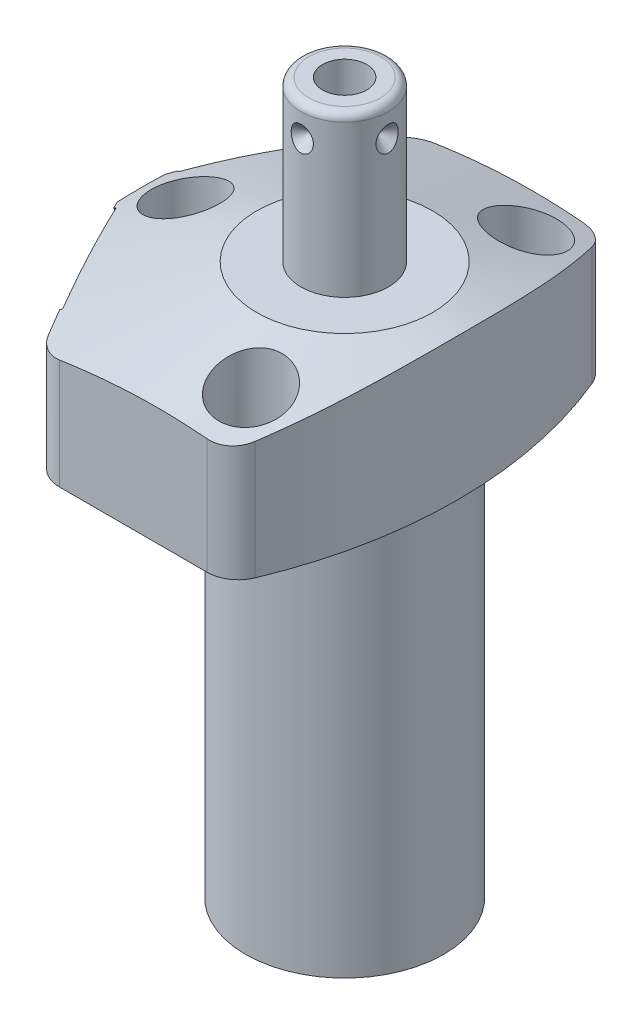
SolidWorks part; units mm, degrees
material "Alloy Steel"
ref_plane "Front Plane" through (0, 0, 0) normal (0, 0, 1) x (1, 0, 0)
ref_plane "Top Plane" through (0, 0, 0) normal (0, 1, 0) x (1, 0, 0)
ref_plane "Right Plane" through (0, 0, 0) normal (1, 0, 0) x (0, 0, -1)
ref_plane "Plane1" through (0, 0, 0) normal (0, 0, 1) x (0, -1, 0)
sketch "Sketch1" plane through (0, 0, 0) normal (0, 0, 1) x (0, -1, 0)
  line L0 (0, 28.575) -> (-19.05, 28.575)
  line L1 (-19.05, 28.575) -> (-19.05, 0)
  line L2 (-19.05, 0) -> (50.8, 0)
  line L3 (50.8, 0) -> (50.8, 12.573)
  line L4 (50.8, 12.573) -> (0, 12.573)
  line L5 (0, 12.573) -> (0, 28.575)
  line L6 (-22.5425, 0) -> (54.2925, 0) construction
  dimension "D1" = 69.85
  dimension "D2" = 19.05
  dimension "D3" = 25.146
  dimension "D4" = 57.15
revolve "Revolve1" add sketch "Sketch1" angle 360 about L6
ref_plane "Plane2" through (0, 0, 0) normal (0, -1, 0) x (0, 0, -1)
sketch "Sketch2" plane through (0, 0, 0) normal (0, -1, 0) x (0, 0, -1)
  line L0 (23.8125, -15.7954) -> (23.8125, 15.7954)
  line L2 (-23.8125, 15.7954) -> (-23.8125, -15.7954)
  line L3 (0, -18.0139) -> (0, 30.7935) construction
  arc A0 (23.8125, -15.7954) -> (23.8125, 15.7954) centre (0, 0) ccw
  circle A1 centre (0, 0) radius 28.575
  arc A2 (-23.8125, 15.7954) -> (-23.8125, -15.7954) centre (0, 0) ccw
  point P4 (0, 0)
  dimension "D1" = 47.625
  dimension "D2" = 0
extrude "Cut-Extrude1" cut sketch "Sketch2" against normal up to next
ref_plane "Plane3" through (0, 0, 0) normal (0, -1, 0) x (-1, 0, 0)
sketch "Sketch3" plane through (0, 0, 0) normal (0, -1, 0) x (-1, 0, 0)
  line L0 (14.7539, 23.8125) -> (27.4152, 0)
  line L1 (27.4152, 0) -> (14.7539, -23.8125)
  line L2 (-24.5787, -13.0687) -> (45.9515, 24.4329) construction
  line L3 (0, 0) -> (35.175, 0) construction
  line L4 (15.7954, -23.8125) -> (-15.7954, -23.8125) construction
  line L5 (-15.7954, 23.8125) -> (15.7954, 23.8125) construction
  line L6 (15.7954, -23.8125) -> (14.7539, -23.8125)
  line L7 (14.7539, 23.8125) -> (15.7954, 23.8125)
  arc A0 (15.7954, -23.8125) -> (15.7954, 23.8125) centre (0, 0) ccw construction
  arc A1 (15.7954, -23.8125) -> (15.7954, 23.8125) centre (0, 0) ccw
  dimension "D1" = 28
  dimension "D2" = 24.2062
extrude "Cut-Extrude2" cut sketch "Sketch3" against normal up to next
ref_plane "Plane4" through (0, 0, 0) normal (0, -1, 0) x (-1, 0, 0)
sketch "S2D0002" plane through (0, 0, 0) normal (0, -1, 0) x (-1, 0, 0)
  line L0 (25.8064, 53.3791) -> (25.8064, -53.3791)
  arc A0 (25.8064, 53.3791) -> (25.8064, -53.3791) centre (41.275, 0) ccw
  dimension "D1" = 55.5752
  dimension "D2" = 15.4686
  dimension "D3" = 41.275
extrude "Cut-Extrude3" cut sketch "S2D0002" against normal blind 26.035 flip side to cut
fillet "Fillet1" radius 3.9624 4 edges at (8.9402, 9.525, 23.8125) (-14.7539, 9.525, 23.8125) (-14.7539, 9.525, -23.8125) (8.9402, 9.525, -23.8125)
ref_plane "Plane5" through (0, 0, 0) normal (0, 0, 1) x (1, 0, 0)
sketch "Sketch5" plane through (0, 0, 0) normal (0, 0, 1) x (1, 0, 0)
  line L0 (-11.176, 19.05) -> (-44.45, 8.2386)
  line L1 (0, 5.9984) -> (0, 19.6715) construction
  line L2 (-15.8716, 19.05) -> (-25.8064, 19.05) construction
  line L3 (-11.176, 19.05) -> (-44.45, 19.05)
  line L4 (-44.45, 19.05) -> (-44.45, 8.2386)
  dimension "D1" = 22.352
  dimension "D2" = 18
  dimension "D3" = 44.45
revolve "Cut-Revolve1" cut sketch "Sketch5" angle 360 about L1
ref_plane "Plane6" through (-21.1485, 7.9502, -11.2449) normal (0, 1, 0) x (0.4695, 0, -0.8829)
sketch "Sketch6" plane through (-21.1485, 7.9502, -11.2449) normal (0, 1, 0) x (0.4695, 0, -0.8829)
  line L0 (0, 0) -> (4.5466, 0)
  line L1 (4.5466, 0) -> (4.1066, -2.0701)
  line L2 (4.1066, -2.0701) -> (3.4544, -2.7223)
  line L3 (3.4544, -2.7223) -> (3.4544, -12.192)
  line L4 (3.4544, -12.192) -> (0, -12.192)
  line L5 (0, -12.192) -> (0, 0)
  line L6 (0, -12.8016) -> (0, 0.6096) construction
  dimension "D1" = 12.192
revolve "Cut-Revolve2" cut sketch "Sketch6" angle 360 about L6
ref_plane "Plane7" through (-21.1485, 7.9502, 11.2449) normal (0, 1, 0) x (-0.4695, 0, -0.8829)
sketch "Sketch7" plane through (-21.1485, 7.9502, 11.2449) normal (0, 1, 0) x (-0.4695, 0, -0.8829)
  line L0 (0, 0) -> (4.5466, 0)
  line L1 (4.5466, 0) -> (4.1066, -2.0701)
  line L2 (4.1066, -2.0701) -> (3.4544, -2.7223)
  line L3 (3.4544, -2.7223) -> (3.4544, -12.192)
  line L4 (3.4544, -12.192) -> (0, -12.192)
  line L5 (0, -12.192) -> (0, 0)
  line L6 (0, -12.8016) -> (0, 0.6096) construction
  dimension "D1" = 12.192
revolve "Cut-Revolve3" cut sketch "Sketch7" angle 360 about L6
ref_plane "Plane8" through (-11.1252, 2.667, -15.875) normal (0, 0, 1) x (-1, 0, 0)
sketch "Sketch17" plane through (-21.3728, 0, 11.3641) normal (-0.8829, 0, 0.4695) x (0.4695, 0, 0.8829)
  circle A0 centre (0, 7.9502) radius 10.4775
  dimension "D1" = 20.955
extrude "Cut-Extrude4" cut sketch "Sketch17" against normal blind 0.254
sketch "Sketch18" plane through (-21.3728, 0, -11.3641) normal (-0.8829, 0, -0.4695) x (-0.4695, 0, 0.8829)
  circle A0 centre (0, 7.9502) radius 10.4775
  dimension "D1" = 20.955
extrude "Cut-Extrude5" cut sketch "Sketch18" against normal blind 0.254
sketch "Sketch8" plane through (-11.1252, 2.667, -15.875) normal (0, 0, 1) x (-1, 0, 0)
  line L0 (0, 0) -> (4.5466, 0)
  line L1 (4.5466, 0) -> (4.1066, -2.0701)
  line L2 (4.1066, -2.0701) -> (3.4544, -2.7223)
  line L3 (3.4544, -2.7223) -> (3.4544, -11.684)
  line L4 (3.4544, -11.684) -> (0, -11.684)
  line L5 (0, -11.684) -> (0, 0)
  line L6 (0, -12.2682) -> (0, 0.5842) construction
  dimension "D1" = 11.684
revolve "Cut-Revolve4" cut sketch "Sketch8" angle 360 about L6
ref_plane "Plane9" through (-11.1252, 2.667, 15.875) normal (0, 0, 1) x (-1, 0, 0)
sketch "Sketch9" plane through (-11.1252, 2.667, 15.875) normal (0, 0, 1) x (-1, 0, 0)
  line L0 (0, 0) -> (4.5466, 0)
  line L1 (4.5466, 0) -> (4.1066, -2.0701)
  line L2 (4.1066, -2.0701) -> (3.4544, -2.7223)
  line L3 (3.4544, -2.7223) -> (3.4544, -11.684)
  line L4 (3.4544, -11.684) -> (0, -11.684)
  line L5 (0, -11.684) -> (0, 0)
  line L6 (0, -12.2682) -> (0, 0.5842) construction
  dimension "D1" = 11.684
revolve "Cut-Revolve5" cut sketch "Sketch9" angle 360 about L6
ref_plane "Plane10" through (0, 0, 0) normal (1, 0, 0) x (0, 0, -1)
sketch "Sketch10" plane through (0, 0, 0) normal (1, 0, 0) x (0, 0, -1)
  line L0 (0, 19.05) -> (-5.5562, 19.05)
  line L1 (-5.5562, 19.05) -> (-5.5562, 38.3032)
  line L2 (-4.5402, 39.3192) -> (0, 39.3192)
  line L3 (0, 39.3192) -> (0, 19.05)
  line L4 (0, 18.0365) -> (0, 44.824) construction
  line L5 (11.176, 19.05) -> (-11.176, 19.05) construction
  line L6 (-21.374, 0) -> (21.374, 0) construction
  arc A0 (-4.5402, 39.3192) -> (-5.5562, 38.3032) centre (-4.5402, 38.3032) ccw
  dimension "D3" = 1.016
  dimension "D1" = 11.1125
  dimension "D2" = 39.3192
revolve "Revolve2" add sketch "Sketch10" angle 360 about L4
sketch "Sketch19" plane through (0, 0, 0) normal (0, -1, 0) x (1, 0, 0)
  circle A0 centre (-11.1252, -15.875) radius 5.5626
  circle A1 centre (-11.1252, 15.875) radius 5.5626
  dimension "D1" = 11.1252
extrude "Cut-Extrude6" cut sketch "Sketch19" against normal blind 2.667
ref_plane "Plane11" through (2.8067, 39.3192, 0) normal (0, 0, 1) x (1, 0, 0)
sketch "S2D0001" plane through (2.8067, 39.3192, 0) normal (0, 0, 1) x (1, 0, 0)
  line L0 (0, 0) -> (0, -10.16)
  line L1 (0, -10.16) -> (-2.8067, -11.8464)
  line L2 (0, 0) -> (-2.8067, 0)
  line L3 (-2.8067, 0) -> (-2.8067, -11.8464)
  line L4 (-2.8067, -17.5667) -> (-2.8067, 0.5923) construction
  line L5 (1.7335, 0) -> (-7.3469, 0) construction
  dimension "D1" = 5.6134
  dimension "D2" = 10.16
  dimension "D3" = 59
revolve "Cut-Revolve6" cut sketch "S2D0001" angle 360 about L4
ref_plane "Plane14" through (-11.1252, 0, 15.875) normal (1, 0, 0) x (0, 0, -1)
sketch "Sketch14" plane through (-11.1252, 0, 15.875) normal (1, 0, 0) x (0, 0, -1)
  line L0 (5.461, 2.667) -> (5.461, 0.9398)
  line L1 (5.461, 0.9398) -> (5.3016, 0.9398)
  line L2 (2.667, 0.4318) -> (2.667, 0.127)
  line L3 (2.667, 0.127) -> (1.5875, 0.127)
  line L4 (1.5875, 0.127) -> (1.5875, 10.6172)
  line L5 (1.5875, 10.6172) -> (3.2512, 10.6172)
  line L6 (3.2512, 10.6172) -> (3.2512, 2.667)
  line L7 (3.2512, 2.667) -> (5.461, 2.667)
  line L8 (3.175, 0.9398) -> (3.8424, 0.9398)
  line L9 (0, -1.0109) -> (0, 11.1709) construction
  line L10 (-3.4544, 14.351) -> (-3.4544, 5.3893) construction
  line L11 (3.4544, 5.3893) -> (3.4544, 14.351) construction
  line L12 (-5.499, 0) -> (37.249, 0) construction
  arc A0 (3.175, 0.9398) -> (2.667, 0.4318) centre (3.175, 0.4318) ccw
  arc A1 (3.8424, 0.9398) -> (5.3016, 0.9398) centre (4.572, 0.4318) ccw
  dimension "D5" = 0.508
  dimension "D9" = 0.889
  dimension "D1" = 2.54
  dimension "D2" = 7.9502
  dimension "D3" = 3.175
  dimension "D4" = 0.127
  dimension "D6" = 5.334
  dimension "D7" = 0.3048
  dimension "D8" = 0.3048
  dimension "D10" = 9.144
  dimension "D11" = 10.922
  dimension "D12" = 6.5024
revolve "Revolve3" add sketch "Sketch14" angle 360 about L9
ref_plane "Plane17" through (0, 0, 0) normal (0, 0, 1) x (1, 0, 0)
ref_plane "Plane15" through (-5.5562, 35.3568, 0) normal (0, 0, 1) x (0, 1, 0)
sketch "Sketch15" plane through (-5.5563, 35.3568, 0) normal (0, 0, 1) x (0, 1, 0)
  line L0 (0, 0) -> (1.5875, 0)
  line L1 (1.5875, 0) -> (0, -1.5875)
  line L2 (0, 0) -> (0, -1.5875)
  line L3 (0, -3.7018) -> (0, 0.0794) construction
  line L4 (2.9464, 0) -> (-16.3068, 0) construction
  line L5 (3.9624, -10.0965) -> (3.9624, -1.016) construction
  dimension "D1" = 3.9624
  dimension "D2" = 3.175
  dimension "D3" = 45
ref_plane "Plane16" through (5.5562, 35.3568, 0) normal (0, 0, 1) x (0, -1, 0)
revolve "Cut-Revolve7" cut sketch "Sketch15" angle 360 about L3
pattern_circular "CirPattern1" count 4 over 360 about axis through (0, 18.0365, 0) along (0, -1, 0) of "Cut-Revolve7"
hole_wizard "Hole1" positions "Sketch21" profile "Sketch20" legacy end condition up to next
sketch "Sketch21" plane through (0, 19.05, 0) normal (0, 1, 0) x (-1, 0, 0)
  line L0 (0, 0) -> (31.1465, 0) construction
  line L1 (0, 0) -> (0, 26.4037) construction
  point P0 (-5.5626, -17.4498)
  point P9 (20.193, 0)
  point P13 (-5.5626, 17.4498)
  dimension "D1" = 5.5626
  dimension "D2" = 17.4498
  dimension "D3" = 20.193
sketch "Sketch20" plane through (5.5626, 19.05, -17.4498) normal (1, 0, 0) x (0, 0, 1)
  line L0 (0, 0) -> (0, 19.05)
  line L1 (0, 19.05) -> (2.7813, 19.05)
  line L2 (2.7813, 19.05) -> (2.7813, 11.0998)
  line L3 (2.7813, 11.0998) -> (4.3561, 11.0998)
  line L4 (4.3561, 11.0998) -> (4.3561, 0)
  line L5 (4.3561, 0) -> (0, 0)
  line L6 (0, 110) -> (0, -10) construction
  dimension "Diameter" = 5.5626
  dimension "Depth" = 19.05
  dimension "C-Bore Diameter" = 8.7122
  dimension "C-Bore Depth" = 11.0998
mirror "Mirror1" about plane through (0, 0, 0) normal (0, 0, 1) of "Revolve3"
